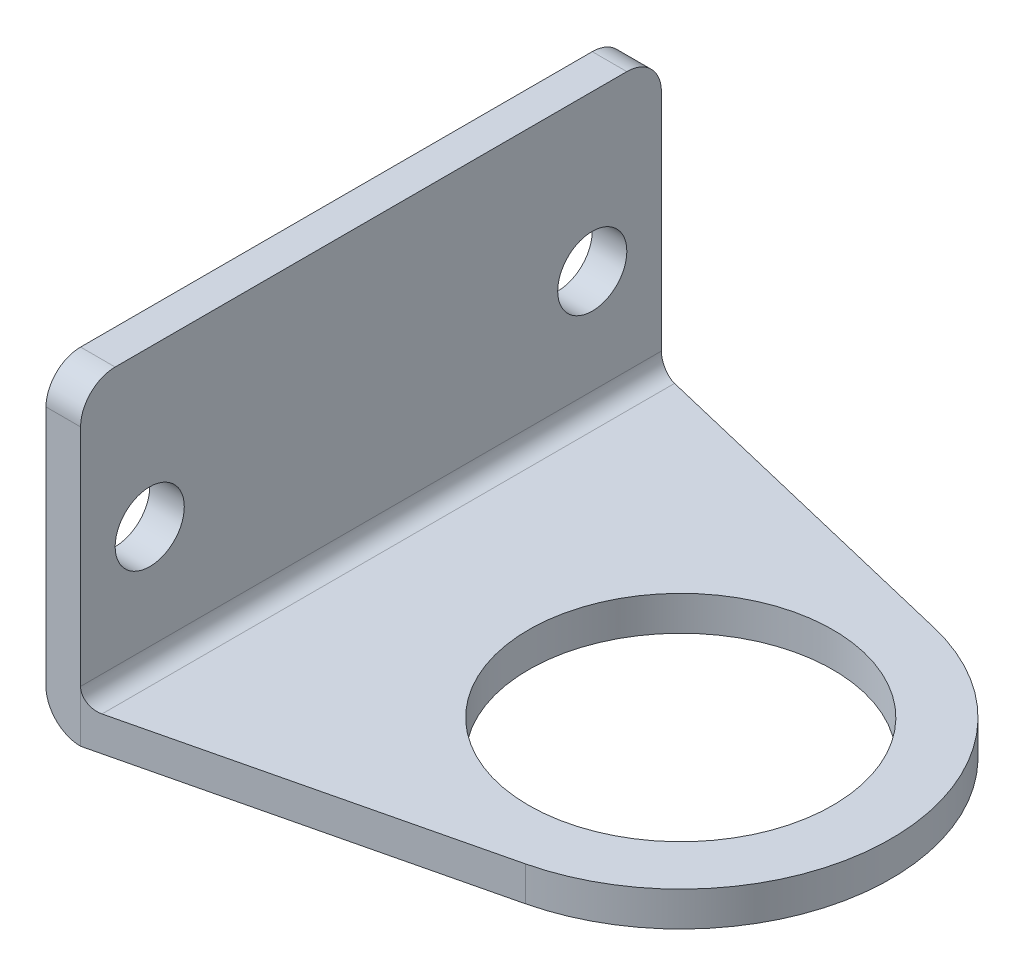
SolidWorks part; units mm, degrees
material "6061-T6 (SS)"
ref_plane "Front Plane" through (0, 0, 0) normal (0, 0, 1) x (1, 0, 0)
ref_plane "Top Plane" through (0, 0, 0) normal (0, 1, 0) x (1, 0, 0)
ref_plane "Right Plane" through (0, 0, 0) normal (1, 0, 0) x (0, 0, -1)
sketch "Sketch1" plane through (0, 0, 0) normal (0, 1, 0) x (1, 0, 0)
  line L0 (0, 0) -> (-28.448, 0)
  line L1 (-28.448, 0) -> (-28.448, 13.97)
  line L2 (-28.448, 13.97) -> (-28.448, -13.97)
  line L3 (-28.448, 13.97) -> (-28.448, 26.67)
  line L4 (-28.448, -13.97) -> (-28.448, -26.67)
  line L5 (-28.448, -26.67) -> (4.4998, -18.7722)
  line L6 (-28.448, 26.67) -> (4.4998, 18.7722)
  line L8 (-28.448, 26.67) -> (-31.623, 26.67)
  line L9 (-28.448, 26.67) -> (-28.448, -26.67)
  line L10 (-28.448, -26.67) -> (-31.623, -26.67)
  line L11 (-31.623, 26.67) -> (-31.623, -26.67)
  circle A0 centre (0, 0) radius 13.97
  circle A1 centre (0, 0) radius 19.304
  dimension "D1" = 38.608
  dimension "D8" = 27.94
  dimension "D2" = 28.448
  dimension "D3" = 13.97
  dimension "D4" = 27.94
  dimension "D5" = 12.7
  dimension "D6" = 12.7
  dimension "D7" = 3.175
extrude "Boss-Extrude1" add sketch "Sketch1" along normal blind 3.175
sketch "Sketch2" plane through (0, 3.175, 0) normal (0, 1, 0) x (1, 0, 0)
  line L0 (-28.448, -26.67) -> (-31.623, -26.67) construction
  line L1 (-28.448, 26.67) -> (-31.623, 26.67) construction
  line L2 (-31.623, 26.67) -> (-31.623, -26.67) construction
  line L3 (-28.448, -26.67) -> (-31.623, -26.67)
  line L4 (-28.448, 26.67) -> (-31.623, 26.67)
  line L5 (-31.623, 26.67) -> (-31.623, -26.67)
  line L7 (-28.448, 26.67) -> (-31.623, 26.67)
  line L8 (-28.448, 26.67) -> (-28.448, -26.67)
  line L9 (-28.448, -26.67) -> (-31.623, -26.67)
  line L10 (-31.623, 26.67) -> (-31.623, -26.67)
  line M4 (-28.448, 26.67) -> (-31.623, 26.67)
  line M5 (-31.623, 26.67) -> (-31.623, -26.67)
  line M6 (-31.623, -26.67) -> (-28.448, -26.67)
extrude "Boss-Extrude2" add sketch "Sketch2" along normal blind 25.4 contours L8 M4 M5 M6
sketch "Sketch6" plane through (-31.623, 0, 0) normal (-1, 0, 0) x (0, 0, 1)
  line L0 (0, 28.575) -> (-13.97, 28.575)
  line L1 (-26.67, 28.575) -> (26.67, 28.575) construction
  line L2 (-26.67, 0) -> (26.67, 0) construction
  line L3 (-13.97, 28.575) -> (13.97, 28.575)
  line L4 (-13.97, 28.575) -> (-13.97, 0)
  line L5 (-13.97, 0) -> (13.97, 0)
  line L6 (13.97, 28.575) -> (13.97, 0)
  line L8 (-26.67, 0) -> (-13.97, 0)
  line L9 (-13.97, 0) -> (-20.32, 0)
  line L10 (-20.32, 0) -> (-20.32, 28.575)
  line L11 (-20.32, 28.575) -> (-20.32, 14.2875)
  line L12 (-20.32, 14.2875) -> (26.67, 14.2875)
  line L13 (26.67, 28.575) -> (26.67, 0) construction
  line L14 (26.67, 14.2875) -> (13.97, 14.2875)
  line L15 (13.97, 14.2875) -> (20.32, 14.2875)
  circle A0 centre (-20.32, 14.2875) radius 3.175
  circle A1 centre (20.32, 14.2875) radius 3.175
  dimension "D1" = 6.35
  dimension "D4" = 6.35
  dimension "D2" = 13.97
  dimension "D3" = 27.94
extrude "Cut-Extrude1" cut sketch "Sketch6" against normal through all contours L10 A0 | L12 A0 L10 | L10 A0 L12 | L14 A1 L15 | L15 A1 L14
fillet "Fillet1" radius 1.5875 1 edges at (-28.448, 3.175, 0)
fillet "Fillet2" radius 3.175 1 edges at (-31.623, 0, 0)
fillet "Fillet3" radius 3.175 2 edges at (-30.0355, 28.575, -26.67) (-30.0355, 28.575, 26.67)
